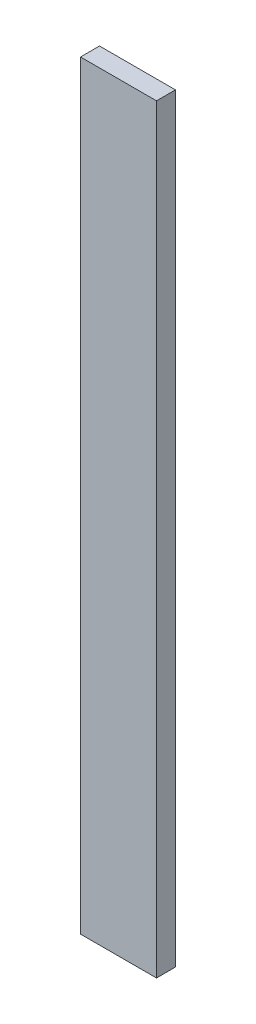
SolidWorks part; units mm, degrees
material "ABS"
ref_plane "Front Plane" through (0, 0, 0) normal (0, 0, 1) x (1, 0, 0)
ref_plane "Top Plane" through (0, 0, 0) normal (0, 1, 0) x (1, 0, 0)
ref_plane "Right Plane" through (0, 0, 0) normal (1, 0, 0) x (0, 0, -1)
sketch "Sketch1" plane through (0, 0, 0) normal (0, 0, 1) x (1, 0, 0)
  line L1 (0, 0) -> (12.7, 0)
  line L2 (0, 0) -> (0, -127)
  line L3 (0, -127) -> (12.7, -127)
  line L4 (12.7, 0) -> (12.7, -127)
  dimension "D1" = 127
  dimension "D2" = 12.7
extrude "Strip" add sketch "Sketch1" along normal blind 3.175
